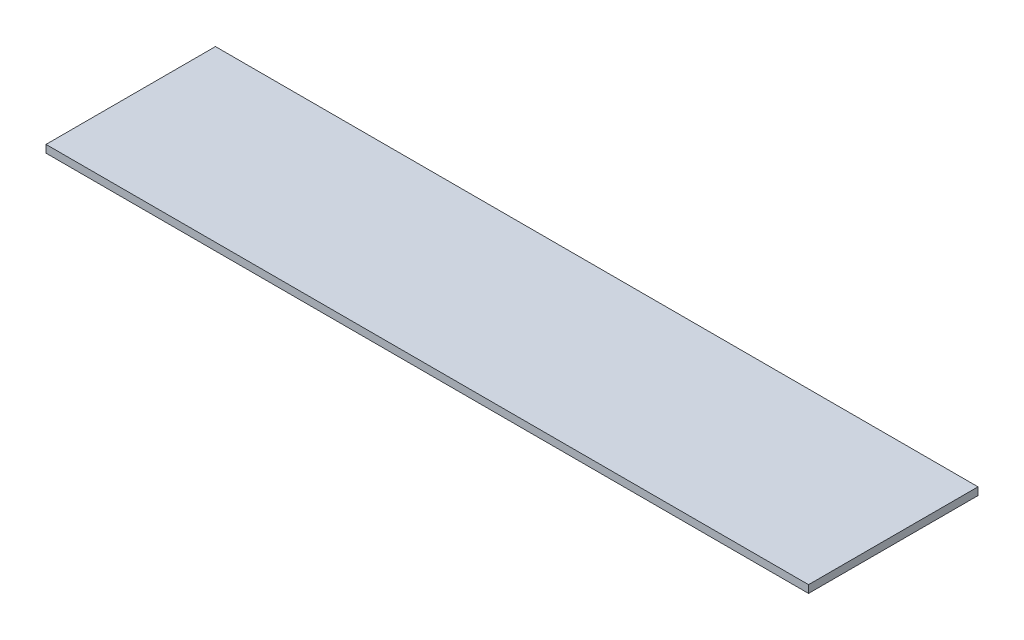
SolidWorks part; units mm, degrees
ref_plane "前视基准面" through (0, 0, 0) normal (0, 0, 1) x (1, 0, 0)
ref_plane "上视基准面" through (0, 0, 0) normal (0, 1, 0) x (1, 0, 0)
ref_plane "右视基准面" through (0, 0, 0) normal (1, 0, 0) x (0, 0, -1)
sketch "草图1" plane through (0, 0, 0) normal (0, 1, 0) x (1, 0, 0)
  line L1 (0, 0) -> (45, 0)
  line L2 (0, 0) -> (0, 10)
  line L3 (0, 10) -> (45, 10)
  line L4 (45, 0) -> (45, 10)
  dimension "D1" = 45
  dimension "D2" = 10
extrude "凸台-拉伸1" add sketch "草图1" along normal blind 0.45
